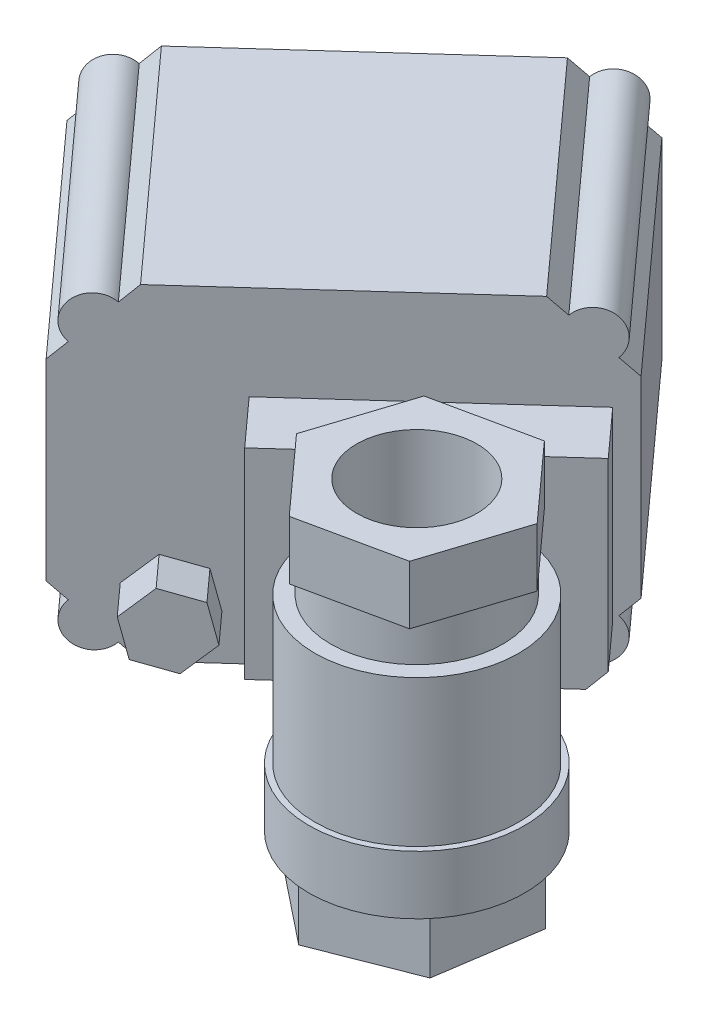
SolidWorks part; units mm, degrees
ref_plane "Front Plane" through (0, 0, 0) normal (0, 0, 1) x (1, 0, 0)
ref_plane "Top Plane" through (0, 0, 0) normal (0, 1, 0) x (1, 0, 0)
ref_plane "Right Plane" through (0, 0, 0) normal (1, 0, 0) x (0, 0, -1)
sketch "Sketch1" plane through (0, 0, 0) normal (0, 1, 0) x (1, 0, 0)
  line L1 (3.6183, -5.1993) -> (5.9072, 10.0276)
  line L2 (5.9072, 10.0276) -> (-6.1352, 19.6233)
  line L3 (-6.1352, 19.6233) -> (-20.4665, 13.9921)
  line L4 (-20.4665, 13.9921) -> (-22.7554, -1.2347)
  line L5 (-22.7554, -1.2347) -> (-10.713, -10.8304)
  line L6 (-10.713, -10.8304) -> (3.6183, -5.1993)
  circle A0 centre (-8.4241, 4.3964) radius 13.335 construction
  dimension "D1" = 26.67
extrude "Boss-Extrude1" add sketch "Sketch1" along normal blind 8.636
sketch "Sketch2" plane through (0, 8.636, 0) normal (0, 1, 0) x (1, 0, 0)
  line L0 (-22.7554, -1.2347) -> (5.9072, 10.0276) construction
  line L1 (-10.713, -10.8304) -> (-6.1352, 19.6233) construction
  circle A0 centre (-8.1163, 4.5174) radius 16.383
extrude "Boss-Extrude2" add sketch "Sketch2" along normal blind 8.89
sketch "Sketch5" plane through (0, 17.526, 0) normal (0, 1, 0) x (1, 0, 0)
  circle A0 centre (-8.1163, 4.5174) radius 15.494
  dimension "D1" = 30.988
extrude "Boss-Extrude3" add sketch "Sketch5" along normal blind 22.225
sketch "Sketch6" plane through (0, 39.751, 0) normal (0, 1, 0) x (1, 0, 0)
  circle A0 centre (-8.1163, 4.5174) radius 13.081
extrude "Boss-Extrude4" add sketch "Sketch6" along normal blind 6.35
sketch "Sketch8" plane through (0, 46.101, 0) normal (0, 1, 0) x (1, 0, 0)
  line L1 (-18.4418, 15.9401) -> (-23.1715, 1.2866)
  line L2 (-23.1715, 1.2866) -> (-12.8459, -10.1362)
  line L3 (-12.8459, -10.1362) -> (2.2092, -6.9054)
  line L4 (2.2092, -6.9054) -> (6.9389, 7.7482)
  line L5 (6.9389, 7.7482) -> (-3.3866, 19.1709)
  line L6 (-3.3866, 19.1709) -> (-18.4418, 15.9401)
  circle A0 centre (-8.1163, 4.5174) radius 13.335 construction
  dimension "D1" = 26.67
extrude "Boss-Extrude5" add sketch "Sketch8" along normal blind 8.89
sketch "Sketch12" plane through (0, 54.991, 0) normal (0, 1, 0) x (1, 0, 0)
  line L0 (-18.4418, 15.9401) -> (2.2092, -6.9054) construction
ref_plane "center plane" through (-2.2194, 0, 2.0062) normal (0.7418, 0, -0.6706) x (-0.6706, 0, -0.7418)
sketch "Sketch18" plane through (0, 54.991, 0) normal (0, 1, 0) x (1, 0, 0)
  line L0 (1.7761, 13.4595) -> (-18.0087, -4.4248) construction
  line L1 (6.9389, 7.7482) -> (-3.3866, 19.1709) construction
  line L2 (-23.1715, 1.2866) -> (-12.8459, -10.1362) construction
ref_plane "Plane2" through (-5.8969, 0, -6.5235) normal (-0.6706, 0, -0.7418) x (-0.7418, 0, 0.6706)
sketch "Sketch24" plane through (-2.2194, 0, 2.0062) normal (0.7418, 0, -0.6706) x (-0.6706, 0, -0.7418)
  line L0 (8.7938, 54.991) -> (8.7938, -4.9314) construction
  line L1 (24.1917, 54.991) -> (-6.6042, 54.991) construction
  line L2 (8.7938, -23.7003) -> (8.7938, 23.7003) construction
sketch "Sketch19" plane through (-5.8969, 0, -6.5235) normal (-0.6706, 0, -0.7418) x (-0.7418, 0, 0.6706)
  line L2 (2.9917, 21.5503) -> (2.9917, -21.5503) construction
  circle A0 centre (2.9917, 28.575) radius 8.509
  dimension "D2" = 17.018
  dimension "D1" = 26.416
extrude "Boss-Extrude9" add sketch "Sketch19" along normal blind 20.574
sketch "Sketch26" plane through (0, 54.991, 0) normal (0, 1, 0) x (1, 0, 0)
  circle A0 centre (-8.1163, 4.5174) radius 9.144
extrude "Cut-Extrude1" cut sketch "Sketch26" against normal through all
sketch "Sketch28" plane through (-19.6934, 0, -21.7861) normal (-0.6706, 0, -0.7418) x (-0.7418, 0, 0.6706)
  line L1 (22.5497, 13.335) -> (-16.5663, 13.335)
  line L2 (22.5497, 13.335) -> (22.5497, 43.815)
  line L3 (22.5497, 43.815) -> (-16.5663, 43.815)
  line L4 (-16.5663, 13.335) -> (-16.5663, 43.815)
  line L5 (22.5497, 13.335) -> (-16.5663, 43.815) construction
  line L6 (22.5497, 43.815) -> (-16.5663, 13.335) construction
  point P0 (2.9917, 28.575)
  dimension "D1" = 39.116
  dimension "D2" = 30.48
extrude "Boss-Extrude11" add sketch "Sketch28" along normal blind 9.525
sketch "Sketch29" plane through (-26.0807, 0, -28.8521) normal (-0.6706, 0, -0.7418) x (-0.7418, 0, 0.6706)
  line L0 (-16.5663, 43.815) -> (-16.5663, 13.335) construction
  line L1 (44.3937, 58.166) -> (-19.6143, 58.166)
  line L2 (44.3937, 58.166) -> (44.3937, 8.636)
  line L3 (44.3937, 8.636) -> (-19.6143, 8.636)
  line L4 (-19.6143, 58.166) -> (-19.6143, 8.636)
  line L5 (44.3937, 58.166) -> (-19.6143, 8.636) construction
  line L6 (44.3937, 8.636) -> (-19.6143, 58.166) construction
  line L7 (-13.3913, 8.636) -> (19.3747, 8.636) construction
  point P0 (12.3897, 33.401)
  dimension "D1" = 64.008
  dimension "D2" = 49.53
  dimension "D3" = 3.048
  dimension "D4" = 0
extrude "Boss-Extrude12" add sketch "Sketch29" along normal blind 44.45
sketch "Sketch31" plane through (-26.0807, 0, -28.8521) normal (0.6706, 0, 0.7418) x (0.7418, 0, -0.6706)
  line L1 (-29.6609, 11.5893) -> (-25.4798, 15.4915)
  line L2 (-25.4798, 15.4915) -> (-26.7687, 21.0636)
  line L3 (-26.7687, 21.0636) -> (-32.2387, 22.7334)
  line L4 (-32.2387, 22.7334) -> (-36.4199, 18.8312)
  line L5 (-36.4199, 18.8312) -> (-35.1309, 13.2591)
  line L6 (-35.1309, 13.2591) -> (-29.6609, 11.5893)
  circle A0 centre (-30.9498, 17.1613) radius 4.953 construction
  dimension "D1" = 9.906
extrude "Boss-Extrude13" add sketch "Sketch31" along normal blind 6.35
sketch "Sketch36" plane through (-55.8879, 0, -61.8268) normal (-0.6706, 0, -0.7418) x (-0.7418, 0, 0.6706)
  line L0 (34.2337, 8.636) -> (34.2337, 58.166) construction
  line L1 (-19.6143, 8.636) -> (44.3937, 8.636) construction
  line L2 (44.3937, 58.166) -> (-19.6143, 58.166) construction
  line L5 (44.3937, 8.636) -> (44.3937, 58.166) construction
  line L6 (-19.6143, 58.166) -> (-19.6143, 8.636) construction
  line L7 (44.3937, 48.006) -> (-19.6143, 48.006) construction
  line L8 (34.2337, 8.636) -> (44.3937, 18.796)
  line L9 (44.3937, 18.796) -> (44.3937, 8.636)
  line L10 (44.3937, 8.636) -> (34.2337, 8.636)
  line L11 (-9.4543, 9.1925) -> (-9.4543, 8.636) construction
  line L12 (-9.4543, 8.636) -> (-19.6143, 18.796)
  line L13 (-9.4543, 8.636) -> (-19.6143, 8.636)
  line L14 (-19.6143, 8.636) -> (-19.6143, 18.796)
  line L15 (-19.6143, 48.006) -> (-9.4543, 58.166)
  line L16 (-9.4543, 58.166) -> (-19.6143, 58.166)
  line L17 (-19.6143, 58.166) -> (-19.6143, 48.006)
  line L18 (44.3937, 48.006) -> (34.2337, 58.166)
  line L19 (34.2337, 58.166) -> (44.3937, 58.166)
  line L20 (44.3937, 58.166) -> (44.3937, 48.006)
  dimension "D1" = 10.16
  dimension "D2" = 10.16
extrude "Cut-Extrude2" cut sketch "Sketch36" against normal up to next
sketch "Sketch37" plane through (-55.8879, 0, -61.8268) normal (-0.6706, 0, -0.7418) x (-0.7418, 0, 0.6706)
  line L0 (39.3137, 8.636) -> (39.3137, 58.166) construction
  line L1 (-9.4543, 8.636) -> (34.2337, 8.636) construction
  line L2 (34.2337, 58.166) -> (-9.4543, 58.166) construction
  line L3 (-14.5343, 8.636) -> (-14.5343, 58.166) construction
  line L4 (44.3937, 13.716) -> (-19.6143, 13.716) construction
  line L5 (44.3937, 18.796) -> (44.3937, 48.006) construction
  line L6 (-19.6143, 48.006) -> (-19.6143, 18.796) construction
  line L7 (44.3937, 53.086) -> (-19.6143, 53.086) construction
  line L8 (44.3937, 18.796) -> (34.2337, 8.636) construction
  line L9 (42.0078, 16.4101) -> (36.6196, 11.0219)
  line L10 (-9.4543, 8.636) -> (-19.6143, 18.796) construction
  line L11 (34.2337, 58.166) -> (44.3937, 48.006) construction
  line L12 (-19.6143, 48.006) -> (-9.4543, 58.166) construction
  line L13 (-11.8402, 11.0219) -> (-17.2284, 16.4101)
  line L14 (-17.2284, 50.3919) -> (-11.8402, 55.7801)
  line L15 (36.6196, 55.7801) -> (42.0078, 50.3919)
  arc A0 (36.6196, 11.0219) -> (42.0078, 16.4101) centre (39.3137, 13.716) ccw
  arc A1 (-17.2284, 16.4101) -> (-11.8402, 11.0219) centre (-14.5343, 13.716) ccw
  arc A2 (42.0078, 50.3919) -> (36.6196, 55.7801) centre (39.3137, 53.086) ccw
  arc A3 (-11.8402, 55.7801) -> (-17.2284, 50.3919) centre (-14.5343, 53.086) ccw
  dimension "D1" = 5.08
  dimension "D2" = 5.08
  dimension "D3" = 5.08
  dimension "D4" = 5.08
extrude "Boss-Extrude14" add sketch "Sketch37" against normal blind 44.45
